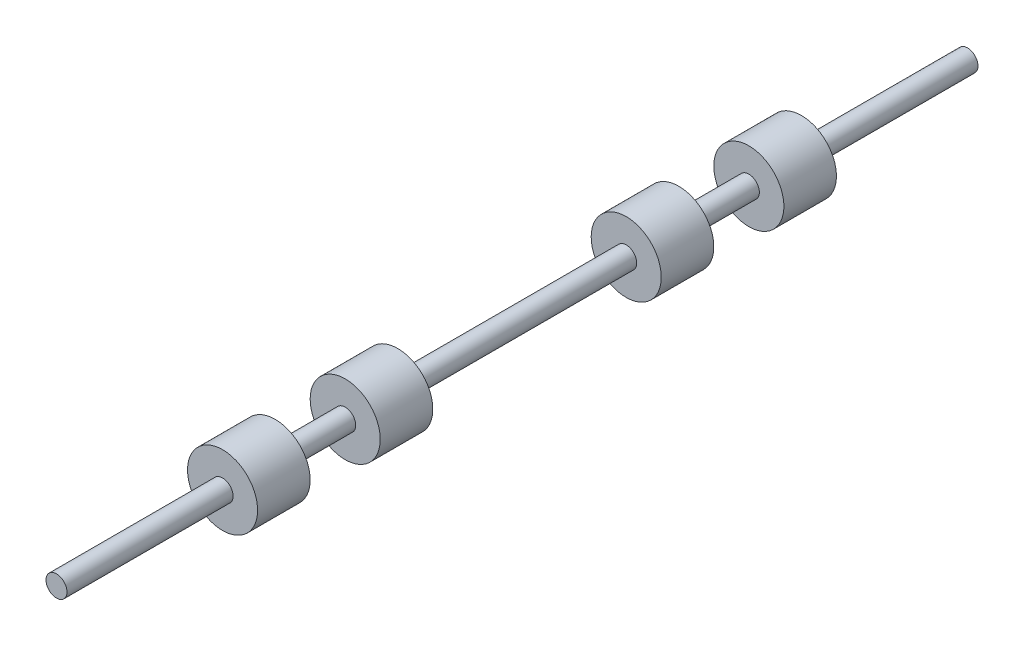
SolidWorks part; units mm, degrees
ref_plane "Front Plane" through (0, 0, 0) normal (0, 0, 1) x (1, 0, 0)
ref_plane "Top Plane" through (0, 0, 0) normal (0, 1, 0) x (1, 0, 0)
ref_plane "Right Plane" through (0, 0, 0) normal (1, 0, 0) x (0, 0, -1)
sketch "Sketch1" plane through (0, 0, 0) normal (0, 0, 1) x (1, 0, 0)
  circle A0 centre (0, 0) radius 0.3
  dimension "D1" = 0.6
extrude "Boss-Extrude1" add sketch "Sketch1" along normal blind 26
sketch "Sketch2" plane through (0, 0, 0) normal (0, 1, 0) x (1, 0, 0)
  line L0 (0, 0) -> (0, -26) construction
  line L1 (-0.3, -26) -> (0.3, -26) construction
  line L2 (0, -7.24) -> (1.591, -7.24) construction
  line L3 (0, -4.74) -> (1, -4.74)
  line L4 (0, -4.74) -> (0, -6.24)
  line L5 (0, -6.24) -> (1, -6.24)
  line L6 (1, -4.74) -> (1, -6.24)
  line L7 (0, -8.24) -> (1, -8.24)
  line L8 (0, -8.24) -> (0, -9.74)
  line L9 (0, -9.74) -> (1, -9.74)
  line L10 (1, -8.24) -> (1, -9.74)
  line L11 (0, -13) -> (7.2023, -13) construction
  line L20 (0, -18.76) -> (2.1947, -18.76) construction
  line L29 (0, -21.26) -> (1, -21.26)
  line L30 (0, -21.26) -> (0, -19.76)
  line L31 (0, -19.76) -> (1, -19.76)
  line L32 (1, -21.26) -> (1, -19.76)
  line L33 (0, -17.76) -> (1, -17.76)
  line L34 (0, -17.76) -> (0, -16.26)
  line L35 (0, -16.26) -> (1, -16.26)
  line L36 (1, -17.76) -> (1, -16.26)
  line L37 (0.3, 0) -> (-0.3, 0) construction
  dimension "D1" = 1.5
  dimension "D2" = 1.5
  dimension "D3" = 1
  dimension "D4" = 1
  dimension "D5" = 2
  dimension "D6" = 1.5
  dimension "D7" = 1.5
  dimension "D8" = 2
  dimension "D9" = 1
  dimension "D10" = 1
  dimension "D11" = 7.24
  dimension "D12" = 7.24
revolve "Revolve1" add sketch "Sketch2" angle 360 about L0
